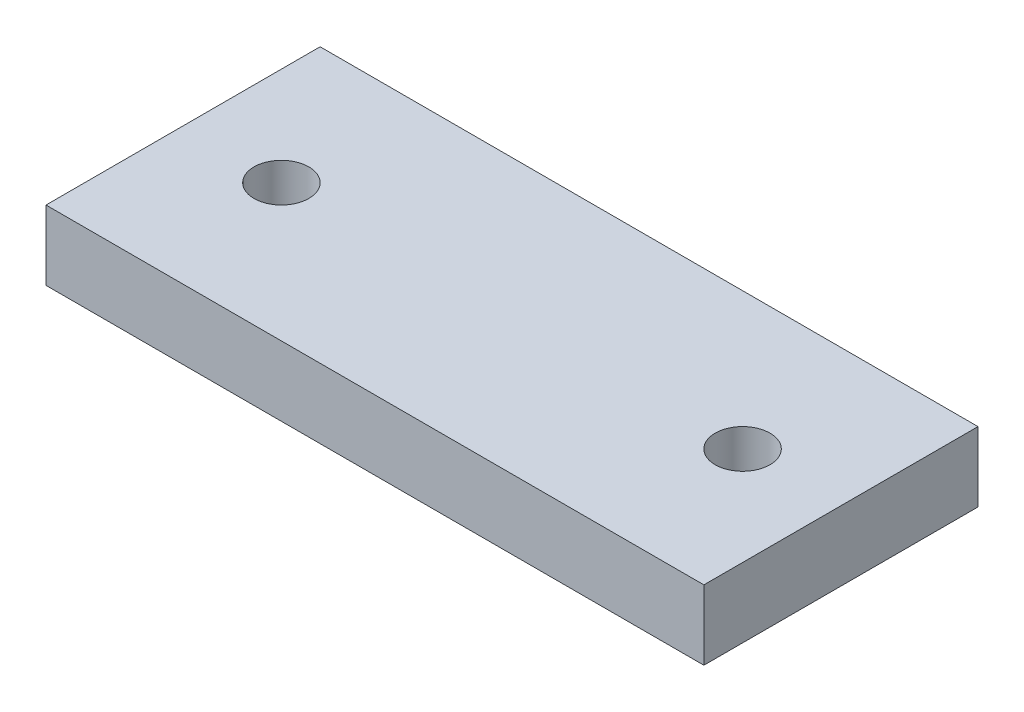
SolidWorks part; units mm, degrees
ref_plane "Front Plane" through (0, 0, 0) normal (0, 0, 1) x (1, 0, 0)
ref_plane "Top Plane" through (0, 0, 0) normal (0, 1, 0) x (1, 0, 0)
ref_plane "Right Plane" through (0, 0, 0) normal (1, 0, 0) x (0, 0, -1)
sketch "Sketch1" plane through (0, 0, 0) normal (0, 1, 0) x (1, 0, 0)
  line L0 (8.97, 12.5) -> (0, 12.5) construction
  line L1 (0, 0) -> (60, 0)
  line L2 (0, 0) -> (0, 25)
  line L3 (0, 25) -> (60, 25)
  line L4 (60, 0) -> (60, 25)
  line L5 (0, 0) -> (60, 25) construction
  line L6 (0, 25) -> (60, 0) construction
  line L7 (51.03, 12.5) -> (60, 12.5) construction
  circle A0 centre (8.97, 12.5) radius 2.5
  circle A1 centre (51.03, 12.5) radius 2.5
  point P4 (30, 12.5)
  dimension "D3" = 42.06
  dimension "D4" = 5
  dimension "D1" = 60
  dimension "D2" = 25
extrude "Boss-Extrude1" add sketch "Sketch1" along normal blind 6.35
